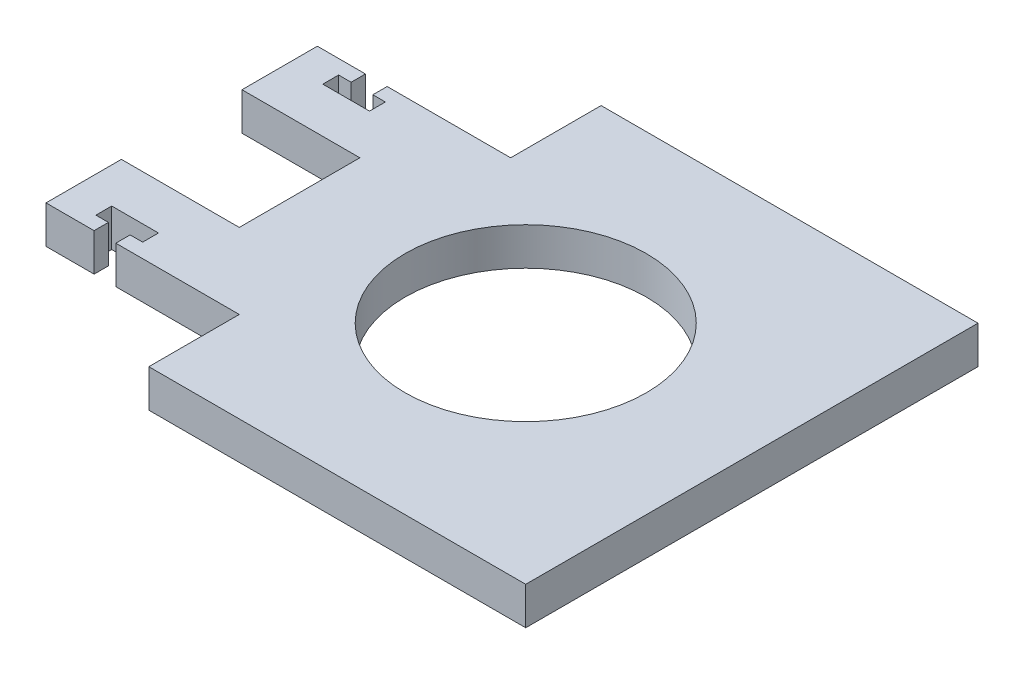
SolidWorks part; units mm, degrees
ref_plane "Front Plane" through (0, 0, 0) normal (0, 0, 1) x (1, 0, 0)
ref_plane "Top Plane" through (0, 0, 0) normal (0, 1, 0) x (1, 0, 0)
ref_plane "Right Plane" through (0, 0, 0) normal (1, 0, 0) x (0, 0, -1)
sketch "Sketch1" plane through (0, 0, 0) normal (0, 1, 0) x (1, 0, 0)
  line L0 (0, 0) -> (38.1, 0) construction
  line L1 (-25.4, -38.1) -> (38.1, -38.1)
  line L3 (-25.4, 38.1) -> (38.1, 38.1)
  line L4 (38.1, -38.1) -> (38.1, 38.1)
  line L5 (-38.1, -38.1) -> (38.1, 38.1) construction
  line L6 (-38.1, 38.1) -> (38.1, -38.1) construction
  line L7 (0, 0) -> (0, -18.5806) construction
  line L8 (-38.1, -22.86) -> (-46.2026, -22.86)
  line L9 (-57.9628, -22.86) -> (-57.9628, -10.16)
  line L10 (-57.9628, -10.16) -> (-38.1, -10.16)
  line L12 (-38.1, 22.86) -> (-46.2026, 22.86)
  line L13 (-57.9628, 10.16) -> (-38.1, 10.16)
  line L14 (-57.9628, 22.86) -> (-57.9628, 10.16)
  line L16 (-38.1, -10.16) -> (-38.1, 10.16)
  line L17 (-48.0314, -24.13) -> (-48.0314, -17.78) construction
  line L19 (-46.2026, -22.86) -> (-46.2026, -20.447)
  line L20 (-46.2026, -20.447) -> (-44.0944, -20.447)
  line L21 (-44.0944, -20.447) -> (-44.0944, -17.78)
  line L22 (-44.0944, -17.78) -> (-51.9684, -17.78)
  line L23 (-49.8602, -22.86) -> (-49.8602, -20.447)
  line L24 (-49.8602, -20.447) -> (-51.9684, -20.447)
  line L25 (-51.9684, -20.447) -> (-51.9684, -17.78)
  line L26 (-49.8602, 20.447) -> (-51.9684, 20.447)
  line L27 (-49.8602, 22.86) -> (-49.8602, 20.447)
  line L28 (-46.2026, 22.86) -> (-46.2026, 20.447)
  line L29 (-46.2026, 20.447) -> (-44.0944, 20.447)
  line L30 (-44.0944, 20.447) -> (-44.0944, 17.78)
  line L31 (-44.0944, 17.78) -> (-51.9684, 17.78)
  line L32 (-51.9684, 20.447) -> (-51.9684, 17.78)
  line L33 (-49.8602, -22.86) -> (-57.9628, -22.86)
  line L34 (-49.8602, 22.86) -> (-57.9628, 22.86)
  line L35 (-38.1, -22.86) -> (-25.4, -22.86)
  line L36 (-25.4, -22.86) -> (-25.4, -38.1)
  line L37 (-25.4, 22.86) -> (-25.4, 38.1)
  line L38 (-38.1, 22.86) -> (-25.4, 22.86)
  circle A0 centre (0, 0) radius 20.32
  point P0 (0, 0)
  point P11 (0, -18.5806)
  point P25 (0, 0)
  point P35 (0, 0)
  dimension "D2" = 40.64
  dimension "D1" = 45
  dimension "D3" = 76.2
  dimension "D4" = 15.24
  dimension "D5" = 20.32
  dimension "D6" = 19.8628
  dimension "D7" = 7.874
  dimension "D8" = 2.667
  dimension "D9" = 5.08
  dimension "D10" = 3.6576
  dimension "D11" = 12.7
extrude "Boss-Extrude1" add sketch "Sketch1" against normal blind 6.35
